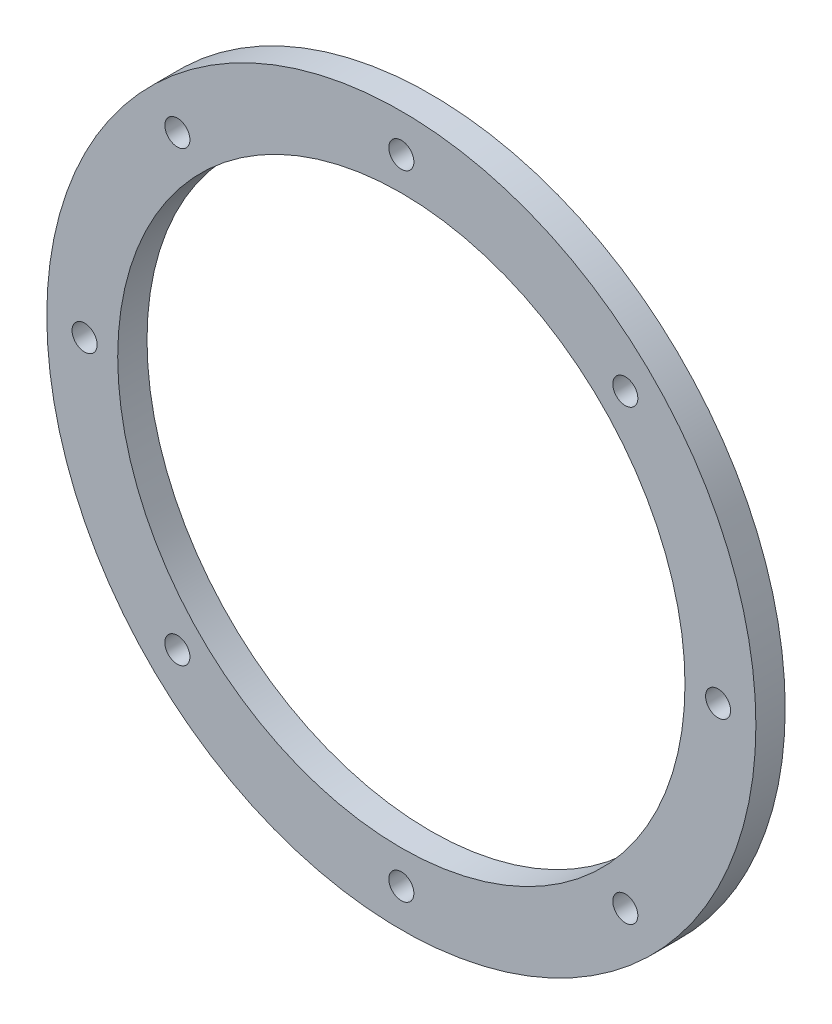
SolidWorks part; units mm, degrees
ref_plane "Front Plane" through (0, 0, 0) normal (0, 0, 1) x (1, 0, 0)
ref_plane "Top Plane" through (0, 0, 0) normal (0, 1, 0) x (1, 0, 0)
ref_plane "Right Plane" through (0, 0, 0) normal (1, 0, 0) x (0, 0, -1)
sketch "Sketch1" plane through (0, 0, 0) normal (0, 0, 1) x (1, 0, 0)
  circle A0 centre (0, 0) radius 76.2
  circle A1 centre (0, 0) radius 95.25
  dimension "D1" = 152.4
  dimension "D2" = 190.5
extrude "Boss-Extrude1" add sketch "Sketch1" along normal blind 7.874
sketch "Sketch2" plane through (0, 0, 7.874) normal (0, 0, 1) x (1, 0, 0)
  circle A0 centre (0, 85.09) radius 3.3655
  dimension "D1" = 6.731
  dimension "D2" = 85.09
extrude "Cut-Extrude1" cut sketch "Sketch2" against normal through all
pattern_circular "CirPattern1" count 8 over 360 about axis through (0, 0, 0) along (0, 0, 1) of "Cut-Extrude1"
